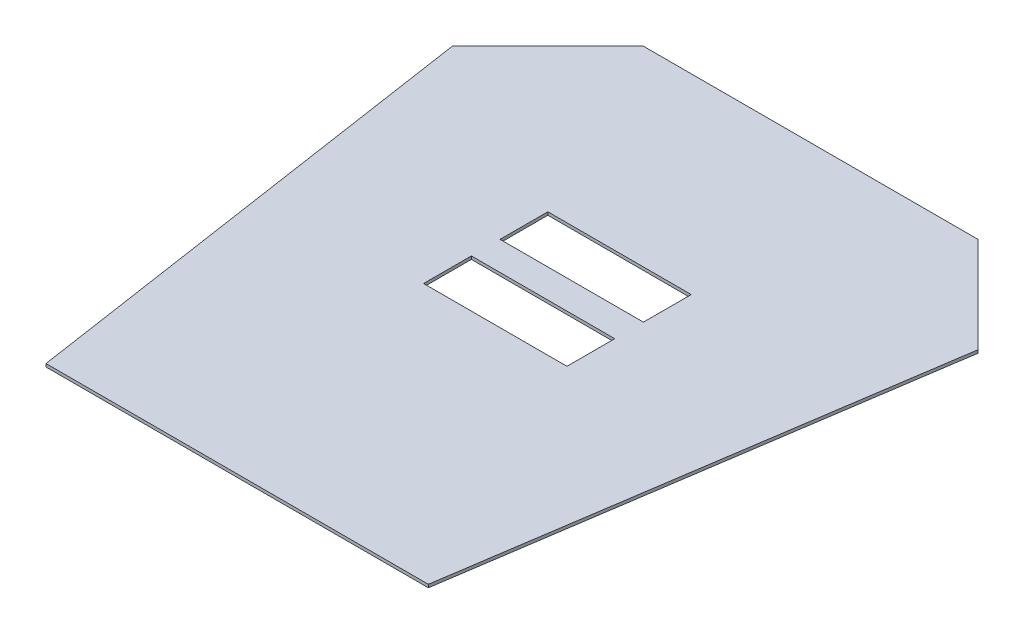
SolidWorks part; units mm, degrees
ref_plane "Front Plane" through (0, 0, 0) normal (0, 0, 1) x (1, 0, 0)
ref_plane "Top Plane" through (0, 0, 0) normal (0, 1, 0) x (1, 0, 0)
ref_plane "Right Plane" through (0, 0, 0) normal (1, 0, 0) x (0, 0, -1)
sketch "Sketch1" plane through (0, 0, 0) normal (0, 1, 0) x (1, 0, 0)
  line L0 (0, 0) -> (0, 180.2923) construction
  line L1 (-175, 100) -> (175, 100)
  line L2 (175, 100) -> (275, 0)
  line L3 (275, 0) -> (200, -500)
  line L4 (200, -500) -> (-200, -500)
  line L5 (-275, 0) -> (-200, -500)
  line L6 (-175, 100) -> (-275, 0)
  point P11 (0, -500)
  point P13 (0, 100)
  dimension "D1" = 175
  dimension "D2" = 100
  dimension "D3" = 100
  dimension "D4" = 600
  dimension "D5" = 75
extrude "Boss-Extrude1" add sketch "Sketch1" along normal blind 3.175
sketch "Sketch2" plane through (0, 3.175, 0) normal (0, 1, 0) x (1, 0, 0)
  line L1 (75, -230) -> (-75, -230)
  line L2 (75, -230) -> (75, -180)
  line L3 (75, -180) -> (-75, -180)
  line L4 (-75, -230) -> (-75, -180)
  line L5 (75, -150) -> (-75, -150)
  line L6 (75, -150) -> (75, -100)
  line L7 (75, -100) -> (-75, -100)
  line L8 (-75, -150) -> (-75, -100)
  point P8 (0, -100)
  dimension "D1" = 150
  dimension "D2" = 50
  dimension "D3" = 30
  dimension "D4" = 100
extrude "Cut-Extrude1" cut sketch "Sketch2" against normal blind 10
